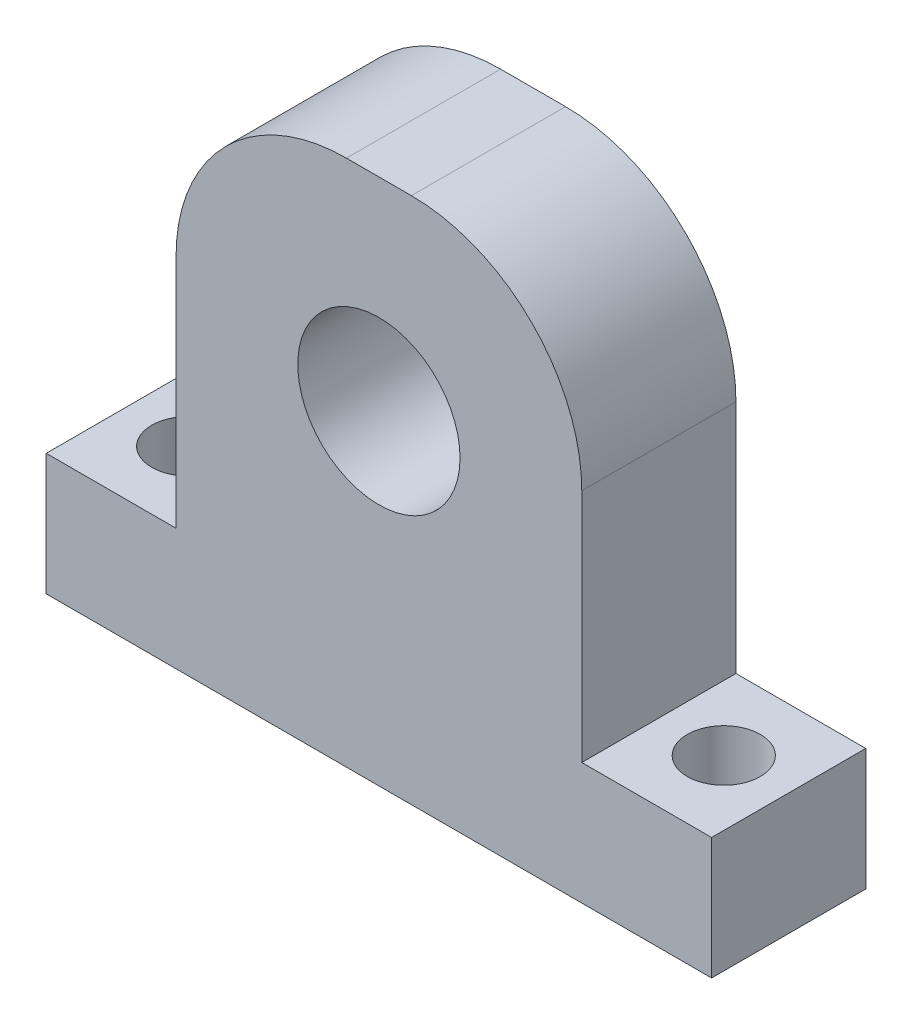
SolidWorks part; units mm, degrees
ref_plane "前视基准面" through (0, 0, 0) normal (0, 0, 1) x (1, 0, 0)
ref_plane "上视基准面" through (0, 0, 0) normal (0, 1, 0) x (1, 0, 0)
ref_plane "右视基准面" through (0, 0, 0) normal (1, 0, 0) x (0, 0, -1)
other "Configuration Table"
sketch "草图1" plane through (0, 0, 0) normal (0, 0, 1) x (1, 0, 0)
  line L0 (0, 0) -> (0, 90.509) construction
  line L1 (-41, 7.5) -> (41, 7.5)
  line L2 (-41, 7.5) -> (-41, -7.5)
  line L3 (-41, -7.5) -> (41, -7.5)
  line L4 (41, 7.5) -> (41, -7.5)
  line L5 (-41, 7.5) -> (41, -7.5) construction
  line L6 (-41, -7.5) -> (41, 7.5) construction
  line L7 (-25, 57.5) -> (25, 57.5)
  line L8 (-25, 57.5) -> (-25, 7.5)
  line L9 (-25, 7.5) -> (25, 7.5)
  line L10 (25, 57.5) -> (25, 7.5)
  line L11 (-25, 57.5) -> (25, 7.5) construction
  line L12 (-25, 7.5) -> (25, 57.5) construction
  circle A1 centre (0, 32.5) radius 10
  point P0 (0, 0)
  point P6 (0, 32.5)
  dimension "D5" = 20
  dimension "D1" = 82
  dimension "D2" = 15
  dimension "D3" = 65
  dimension "D4" = 50
extrude "凸台-拉伸1" add sketch "草图1" along normal blind 19
fillet "圆角1" radius 21 1 edges at (-25, 57.5, 9.5)
fillet "圆角3" radius 21 1 edges at (25, 57.5, 9.5)
sketch "草图2" plane through (0, -7.5, 0) normal (0, -1, 0) x (1, 0, 0)
  line L0 (0, 0) -> (0, 19) construction
  line L1 (-41, 19) -> (41, 19) construction
  line L2 (-41, 9.5) -> (41, 9.5) construction
  line L3 (-41, 19) -> (-41, 0) construction
  line L4 (41, 19) -> (41, 0) construction
  circle A0 centre (-33, 9.5) radius 4.5
  circle A1 centre (33, 9.5) radius 4.5
  dimension "D1" = 33
extrude "切除-拉伸1" cut sketch "草图2" against normal blind 19
